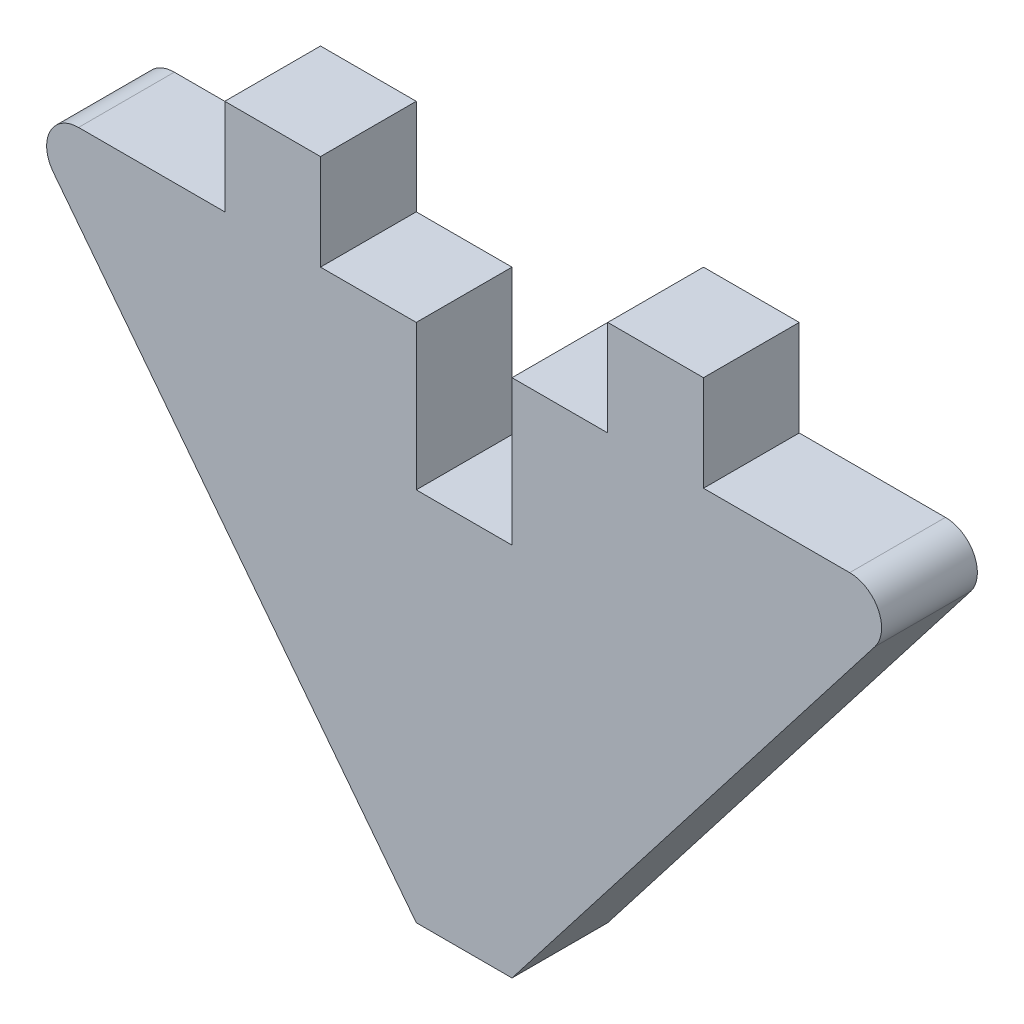
SolidWorks part; units mm, degrees
ref_plane "Front Plane" through (0, 0, 0) normal (0, 0, 1) x (1, 0, 0)
ref_plane "Top Plane" through (0, 0, 0) normal (0, 1, 0) x (1, 0, 0)
ref_plane "Right Plane" through (0, 0, 0) normal (1, 0, 0) x (0, 0, -1)
sketch "Sketch1" plane through (0, 0, 0) normal (0, 0, 1) x (1, 0, 0)
  line L0 (1.524, 62.1762) -> (1.524, 64.4845)
  line L1 (1.524, 64.4845) -> (3.048, 64.4845)
  line L2 (3.048, 64.4845) -> (3.048, 66.0085)
  line L3 (3.048, 66.0085) -> (4.572, 66.0085)
  line L4 (4.572, 66.0085) -> (4.572, 64.4845)
  line L5 (4.572, 64.4845) -> (6.8989, 64.4845)
  line L6 (7.3004, 63.6653) -> (1.524, 56.2096)
  line L7 (1.524, 62.1762) -> (0, 62.1762)
  line L8 (0, 62.1762) -> (1.524, 62.1762) construction
  line L9 (1.524, 56.2096) -> (0, 56.2096)
  line L10 (0, 56.2096) -> (1.524, 56.2096) construction
  line L11 (0.762, 56.2096) -> (0.762, 57.4472) construction
  line L12 (-5.7764, 63.6653) -> (0, 56.2096)
  line L13 (-3.048, 64.4845) -> (-5.3749, 64.4845)
  line L14 (-3.048, 66.0085) -> (-3.048, 64.4845)
  line L15 (-1.524, 66.0085) -> (-3.048, 66.0085)
  line L16 (-1.524, 64.4845) -> (-1.524, 66.0085)
  line L17 (0, 64.4845) -> (-1.524, 64.4845)
  line L18 (0, 62.1762) -> (0, 64.4845)
  arc A0 (-5.7764, 63.6653) -> (-5.3749, 64.4845) centre (-5.3749, 63.9765) cw
  arc A1 (6.8989, 64.4845) -> (7.3004, 63.6653) centre (6.8989, 63.9765) cw
  point P19 (0.762, 62.1762)
  point P27 (-6.4111, 64.4845)
  point P30 (7.9351, 64.4845)
  dimension "D3" = 0.508
  dimension "D1" = 1.524
  dimension "D2" = 1.524
extrude "Boss-Extrude1" add sketch "Sketch1" along normal blind 1.524
